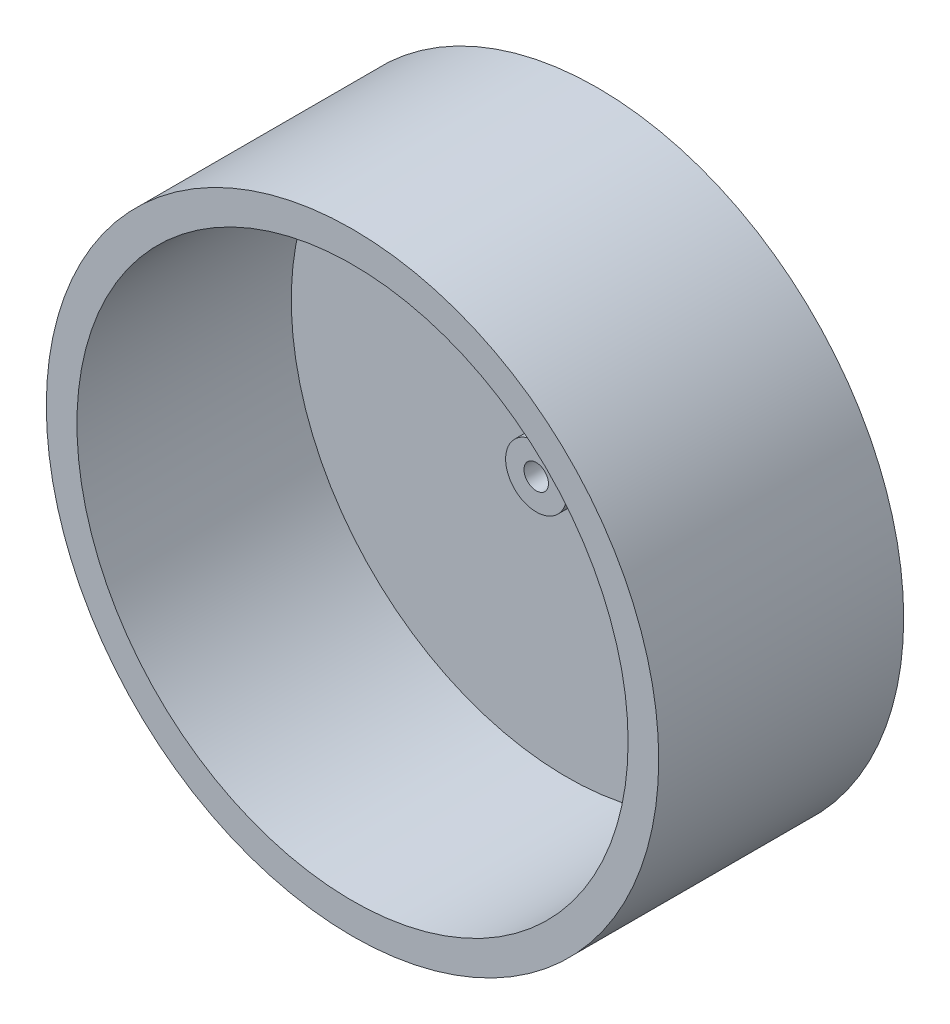
SolidWorks part; units mm, degrees
ref_plane "Front Plane" through (0, 0, 0) normal (0, 0, 1) x (1, 0, 0)
ref_plane "Top Plane" through (0, 0, 0) normal (0, 1, 0) x (1, 0, 0)
ref_plane "Right Plane" through (0, 0, 0) normal (1, 0, 0) x (0, 0, -1)
sketch "Sketch1" plane through (0, 0, 0) normal (0, 0, 1) x (1, 0, 0)
  circle A0 centre (0, 0) radius 50
  dimension "D1" = 100
extrude "Boss-Extrude1" add sketch "Sketch1" along normal blind 40
shell "Shell1" thickness 5
sketch "Sketch2" plane through (0, 0, 5) normal (0, 0, 1) x (1, 0, 0)
  circle A0 centre (0, 0) radius 2
  dimension "D1" = 4
extrude "Cut-Extrude1" cut sketch "Sketch2" against normal through all both and the other way through all
sketch "Sketch3" plane through (0, 0, 5) normal (0, 0, 1) x (1, 0, 0)
  circle A0 centre (0, 0) radius 5
  circle A1 centre (0, 0) radius 2
  dimension "D1" = 10
  dimension "D2" = 4
extrude "Boss-Extrude2" add sketch "Sketch3" along normal blind 5
